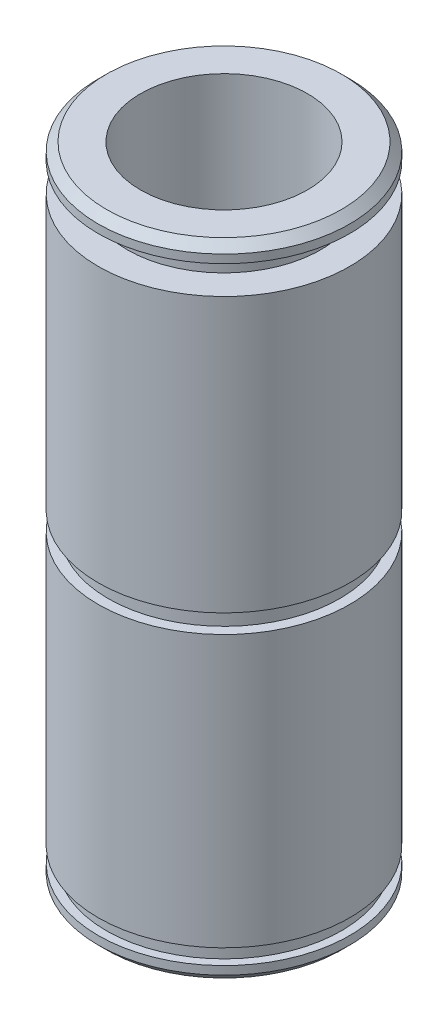
SolidWorks part; units mm, degrees
material "7075-T6 (SN)"
ref_plane "Front Plane" through (0, 0, 0) normal (0, 0, 1) x (1, 0, 0)
ref_plane "Top Plane" through (0, 0, 0) normal (0, 1, 0) x (1, 0, 0)
ref_plane "Right Plane" through (0, 0, 0) normal (1, 0, 0) x (0, 0, -1)
ref_axis "Axis1" through (0, 55, 0) along (0, -1, 0)
sketch "Sketch1" plane through (0, 0, 0) normal (0, 0, 1) x (1, 0, 0)
  line L0 (-9.5631, 24.4958) -> (-9.5631, 45.3339)
  line L1 (-6.35, 0) -> (-9.5631, 0)
  line L2 (-6.35, 0) -> (-6.35, 48.7629)
  line L3 (-6.35, 48.7629) -> (-9.5631, 48.7629)
  line L4 (-9.5631, 0) -> (-9.5631, 1.27)
  line L5 (-9.5631, 1.27) -> (-8.9408, 1.27)
  line L6 (-9.5631, 47.4929) -> (-9.5631, 48.7629)
  line L7 (-9.5631, 2.4384) -> (-8.9408, 2.4384)
  line L8 (-8.9408, 1.27) -> (-8.9408, 2.4384)
  line L9 (-9.5631, 47.4929) -> (-7.366, 47.4929)
  line L10 (0, 55) -> (0, -55) construction
  line L11 (-9.5631, 45.3339) -> (-7.366, 45.3339)
  line L12 (-7.366, 47.4929) -> (-7.366, 45.3339)
  line L13 (-9.5631, 24.4958) -> (-8.8011, 24.4958)
  line L14 (-9.5631, 2.4384) -> (-9.5631, 23.0734)
  line L15 (-9.5631, 23.0734) -> (-8.8011, 23.0734)
  line L16 (-8.8011, 24.4958) -> (-8.8011, 23.0734)
  dimension "D1" = 6.35
  dimension "D2" = 9.5631
  dimension "D3" = 48.7629
  dimension "D4" = 1.27
  dimension "D5" = 2.159
  dimension "D6" = 7.366
  dimension "D7" = 1.27
  dimension "D8" = 23.0734
  dimension "D9" = 1.4224
  dimension "D10" = 8.8011
  dimension "D11" = 1.1684
  dimension "D12" = 8.9408
revolve "Revolve1" add sketch "Sketch1" angle 360 about axis through (0, 55, 0) along (0, -1, 0)
chamfer "Chamfer1" distance 0.635 angle 45 2 edges at (0, 0, 9.5631) (0, 48.7629, 9.5631)
